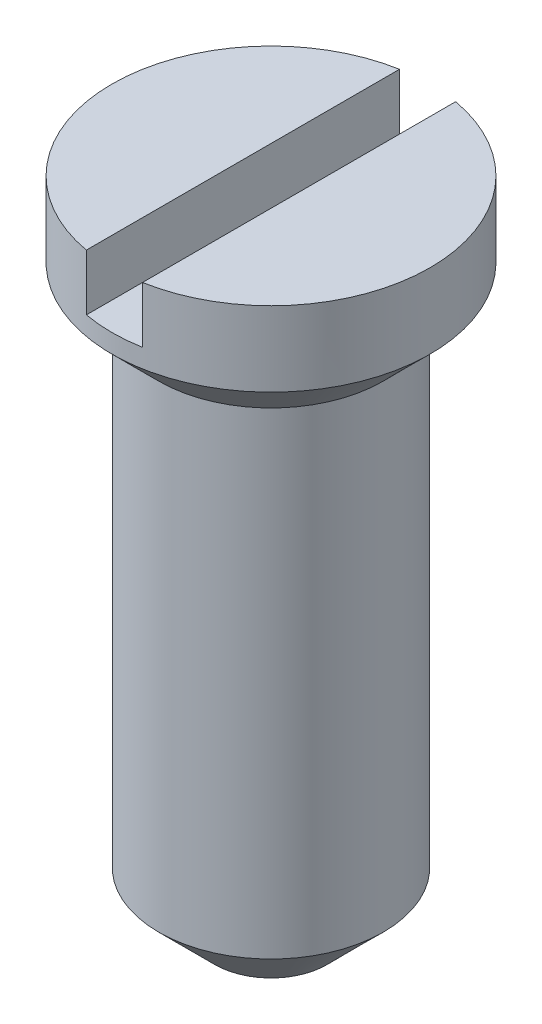
SolidWorks part; units mm, degrees
ref_plane "Front Plane" through (0, 0, 0) normal (0, 0, 1) x (1, 0, 0)
ref_plane "Top Plane" through (0, 0, 0) normal (0, 1, 0) x (1, 0, 0)
ref_plane "Right Plane" through (0, 0, 0) normal (1, 0, 0) x (0, 0, -1)
sketch "Sketch2" plane through (0, 0, 0) normal (0, 1, 0) x (1, 0, 0)
  circle A0 centre (0, 0) radius 0.85
  dimension "D1" = 1.7
extrude "Boss-Extrude1" add sketch "Sketch2" along normal blind 3.5
sketch "Sketch3" plane through (0, 0, 0) normal (0, 0, 1) x (1, 0, 0)
  line L0 (0, 0) -> (0, 3.5) construction
  line L1 (0.85, 3.5) -> (-0.85, 3.5) construction
  line L2 (0.85, 3.1) -> (0.6, 2.85)
  line L3 (0.6, 2.85) -> (0.6, 0)
  line L4 (-0.85, 0) -> (0.85, 0) construction
  line L5 (0.85, 0) -> (0.85, 3.5) construction
  line L6 (0.85, 0) -> (0.85, 3.1)
  line L7 (0.6, 0) -> (0.85, 0)
  dimension "D1" = 1.2
  dimension "D2" = 45
  dimension "D3" = 0.4
revolve "Cut-Revolve1" cut sketch "Sketch3" angle 360 about L0
cosmetic thread "Cosmetic Thread1" parameters "D2"=0.911
sketch "Sketch4" plane through (0, 3.5, 0) normal (0, 1, 0) x (1, 0, 0)
  line L1 (-0.15, -0.95) -> (0.15, -0.95)
  line L2 (-0.15, -0.95) -> (-0.15, 0.95)
  line L3 (-0.15, 0.95) -> (0.15, 0.95)
  line L4 (0.15, -0.95) -> (0.15, 0.95)
  line L5 (-0.15, -0.95) -> (0.15, 0.95) construction
  line L6 (-0.15, 0.95) -> (0.15, -0.95) construction
  circle A2 centre (0, 0) radius 0.85 construction
  point P0 (0, 0)
  dimension "D1" = 0.3
  dimension "D2" = 0.1
extrude "Cut-Extrude1" cut sketch "Sketch4" against normal blind 0.3
chamfer "Chamfer1" distance 0.3 angle 45 1 edges at (0, 0, -0.6)
